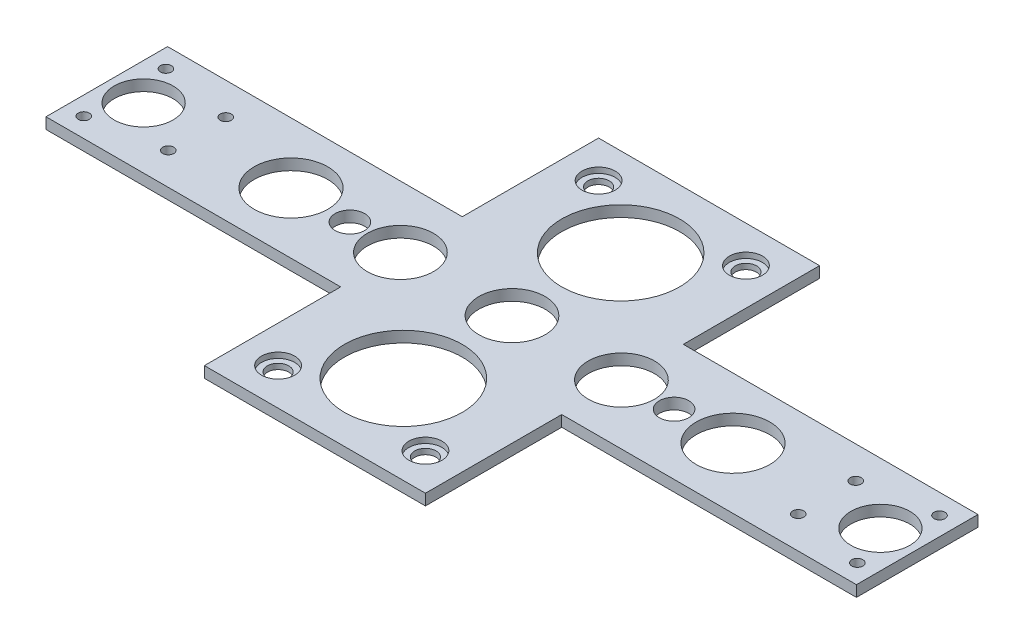
SolidWorks part; units mm, degrees
ref_plane "前视基准面" through (0, 0, 0) normal (0, 0, 1) x (1, 0, 0)
ref_plane "上视基准面" through (0, 0, 0) normal (0, 1, 0) x (1, 0, 0)
ref_plane "右视基准面" through (0, 0, 0) normal (1, 0, 0) x (0, 0, -1)
sketch "草图1" plane through (0, 0, 0) normal (0, 1, 0) x (1, 0, 0)
  line L0 (0, 0) -> (80, 0)
  line L1 (140, 0) -> (220, 0)
  line L2 (0, 0) -> (0, -33)
  line L3 (0, -33) -> (80, -33)
  line L4 (220, 0) -> (220, -33)
  line L5 (140, -33) -> (220, -33)
  line L6 (80, 37) -> (80, 0)
  line L7 (80, -33) -> (80, -70)
  line L8 (140, -33) -> (140, -70)
  line L9 (140, 37) -> (140, 0)
  line L10 (110, -16.5) -> (154, -16.5) construction
  line L11 (110, 37) -> (140, 37)
  line L12 (110, -16.5) -> (66, -16.5) construction
  line L13 (140, -70) -> (80, -70)
  line L15 (80, 37) -> (110, 37)
  circle A0 centre (5, -27.75) radius 1.5
  circle A1 centre (5, -5.45) radius 1.5
  circle A2 centre (24.5, -8.7) radius 1.5
  circle A3 centre (24.5, -24.3) radius 1.5
  circle A4 centre (195.5, -8.7) radius 1.5
  circle A5 centre (195.5, -24.3) radius 1.5
  circle A6 centre (215, -27.75) radius 1.5
  circle A7 centre (215, -5.45) radius 1.5
  circle A8 centre (110, -16.5) radius 9
  circle A9 centre (140, -16.7965) radius 9
  circle A10 centre (10, -16.5) radius 8
  circle A11 centre (210, -16.5) radius 8
  circle A12 centre (170, -16.5) radius 10
  circle A13 centre (80, -16.7965) radius 9
  circle A14 centre (50, -16.5) radius 10
  circle A15 centre (130, 27) radius 2.9
  circle A16 centre (90, 27) radius 2.9
  circle A17 centre (130, -60) radius 2.9
  circle A18 centre (90, -60) radius 2.9
  circle A19 centre (110, 13) radius 16
  circle A20 centre (110, -46) radius 16
  circle A21 centre (66, -16.5) radius 4
  circle A22 centre (154, -16.5) radius 4
  point P45 (140, -33)
  point P51 (80, -33)
  point P52 (80, 0)
  point P53 (140, 0)
extrude "凸台-拉伸1" add sketch "草图1" along normal blind 3
sketch "草图2" plane through (0, 3, 0) normal (0, 1, 0) x (1, 0, 0)
  circle A0 centre (90, 27) radius 4.5
  circle A1 centre (130, 27) radius 4.5
  circle A2 centre (90, -60) radius 4.5
  circle A3 centre (130, -60) radius 4.5
extrude "切除-拉伸1" cut sketch "草图2" along direction (0, 1, 0) on the side against the normal offset from surface (1.5 mm away) 1.5
